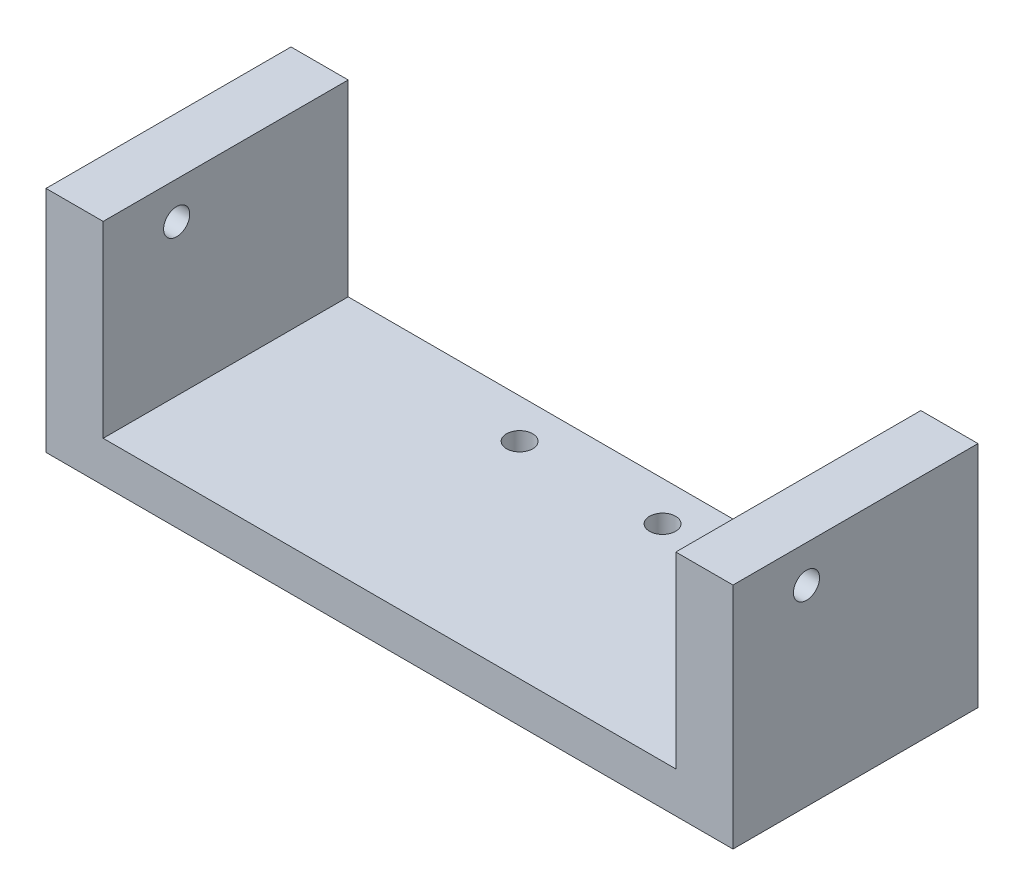
SolidWorks part; units mm, degrees
ref_plane "Front Plane" through (0, 0, 0) normal (0, 0, 1) x (1, 0, 0)
ref_plane "Top Plane" through (0, 0, 0) normal (0, 1, 0) x (1, 0, 0)
ref_plane "Right Plane" through (0, 0, 0) normal (1, 0, 0) x (0, 0, -1)
sketch "Sketch1" plane through (0, 0, 0) normal (0, 1, 0) x (1, 0, 0)
  line L0 (0, 49.8437) -> (0, -62.7125) construction
  line L1 (-73.7687, 0) -> (75.7625, 0) construction
  line L3 (-47.85, -50) -> (47.85, -50)
  line L4 (-47.85, -50) -> (-47.85, 50)
  line L5 (-47.85, 50) -> (47.85, 50)
  line L6 (47.85, -50) -> (47.85, 50)
  line L7 (-47.85, -50) -> (47.85, 50) construction
  line L8 (-47.85, 50) -> (47.85, -50) construction
  circle A0 centre (-8.75, 45.1814) radius 1.6
  circle A1 centre (8.75, 45.1814) radius 1.6
  circle A2 centre (0, -46) radius 1.6
  point P4 (0, 0)
  dimension "D3" = 3.2
  dimension "D5" = 3.2
  dimension "D1" = 95.7
  dimension "D2" = 100
  dimension "D4" = 17.5
  dimension "D6" = 4
extrude "Boss-Extrude1" add sketch "Sketch1" along normal mid plane 6
sketch "Sketch2" plane through (0, 3, 0) normal (0, 1, 0) x (1, 0, 0)
  line L0 (47.85, 50) -> (-47.85, 50) construction
  line L1 (-41.5596, 50) -> (42.555, 50)
  line L2 (-41.5596, 50) -> (-41.5596, 20)
  line L3 (-41.5596, 20) -> (42.555, 20)
  line L4 (42.555, 50) -> (42.555, 20)
  dimension "D1" = 30
extrude "Boss-Extrude2" add sketch "Sketch2" along normal blind 5
sketch "Sketch3" plane through (0, 8, 0) normal (0, 1, 0) x (1, 0, 0)
  line L0 (42.555, 50) -> (42.555, 20) construction
  line L1 (-41.5596, 50) -> (-34.5596, 50)
  line L2 (-41.5596, 50) -> (-41.5596, 20)
  line L3 (-41.5596, 20) -> (-34.5596, 20)
  line L4 (-34.5596, 50) -> (-34.5596, 20)
  line L5 (42.555, 50) -> (35.555, 50)
  line L6 (42.555, 50) -> (42.555, 20)
  line L7 (42.555, 20) -> (35.555, 20)
  line L8 (35.555, 50) -> (35.555, 20)
  line L9 (-41.5596, 20) -> (42.555, 20) construction
  line L10 (-41.5596, 20) -> (42.555, 20) construction
  dimension "D1" = 7
  dimension "D2" = 7
  dimension "D3" = 30
extrude "Boss-Extrude3" add sketch "Sketch3" along normal blind 23
sketch "Sketch4" plane through (-41.5596, 0, 0) normal (-1, 0, 0) x (0, 0, 1)
  line L0 (-35, 42.9747) -> (-35, 14.4749) construction
  line L1 (-20, 31) -> (-20, 3) construction
  circle A1 centre (-29, 26.4748) radius 1.6
  dimension "D1" = 3.2
  dimension "D2" = 9
extrude "Cut-Extrude1" cut sketch "Sketch4" against normal blind 114
sketch "Sketch5" plane through (0, 0, 50) normal (0, 0, 1) x (1, 0, 0)
  line L4 (-47.85, -3) -> (47.85, -3)
  line L5 (47.85, -3) -> (47.85, 3)
  line L6 (47.85, 3) -> (-47.85, 3)
  line L7 (-47.85, 3) -> (-47.85, -3)
  line L8 (-47.85, -3) -> (47.85, -3)
  line L9 (47.85, -3) -> (47.85, 3)
  line L10 (47.85, 3) -> (-47.85, 3)
  line L11 (-47.85, 3) -> (-47.85, -3)
  dimension "D1" = 0
extrude "Cut-Extrude2" cut sketch "Sketch5" against normal blind 114
